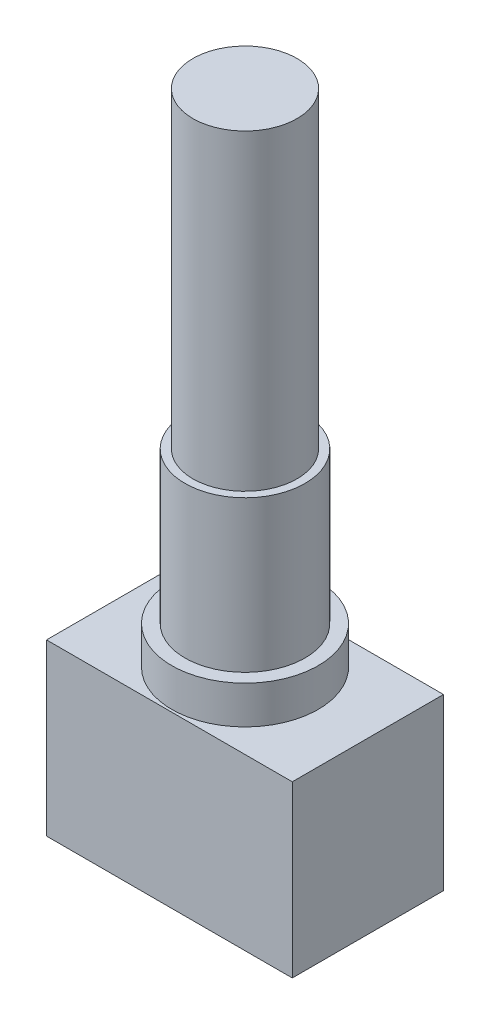
SolidWorks part; units mm, degrees
ref_plane "Front Plane" through (0, 0, 0) normal (0, 0, 1) x (1, 0, 0)
ref_plane "Top Plane" through (0, 0, 0) normal (0, 1, 0) x (1, 0, 0)
ref_plane "Right Plane" through (0, 0, 0) normal (1, 0, 0) x (0, 0, -1)
sketch "Sketch2" plane through (0, 0, 0) normal (0, 0, 1) x (1, 0, 0)
  line L14 (-6.5024, 0) -> (6.5024, 0)
  line L15 (-6.5024, 0) -> (-6.5024, -8.9916)
  line L16 (-6.5024, -8.9916) -> (6.5024, -8.9916)
  line L17 (6.5024, 0) -> (6.5024, -8.9916)
  point P4 (0, 0)
  dimension "D1" = 8.9916
  dimension "D2" = 13.0048
extrude "Boss-Extrude1" add sketch "Sketch2" along normal mid plane 8.001
sketch "Sketch3" plane through (0, 0, 0) normal (0, 0, 1) x (1, 0, 0)
  line L0 (0, 0) -> (0, 50000) construction
  line L1 (3.175, 10.0076) -> (-3.175, 10.0076) construction
  line L2 (-3.175, 10.0076) -> (-3.175, 2.0066)
  line L3 (-3.175, 2.0066) -> (-3.875, 2.0066)
  line L4 (-3.875, 2.0066) -> (-3.875, 0)
  line L5 (6.5024, 0) -> (-6.5024, 0) construction
  line L6 (-3.875, 0) -> (3.875, 0) construction
  line L7 (3.875, 0) -> (3.875, 2.0066) construction
  line L8 (3.875, 2.0066) -> (3.175, 2.0066) construction
  line L9 (3.175, 2.0066) -> (3.175, 10.0076) construction
  line L10 (-3.175, 10.0076) -> (0, 10.0076)
  line L11 (0, 10.0076) -> (0, 0)
  line L12 (0, 0) -> (-3.875, 0)
  dimension "D1" = 2.0066
  dimension "D2" = 8.001
  dimension "D3" = 6.35
  dimension "D4" = 0.7
revolve "Revolve2" add sketch "Sketch3" angle 360 about L0
sketch "Sketch4" plane through (0, 10.0076, 0) normal (0, 1, 0) x (1, 0, 0)
  circle A0 centre (0, 0) radius 2.7559
  dimension "D1" = 5.5118
extrude "Boss-Extrude2" add sketch "Sketch4" along normal blind 16.51
